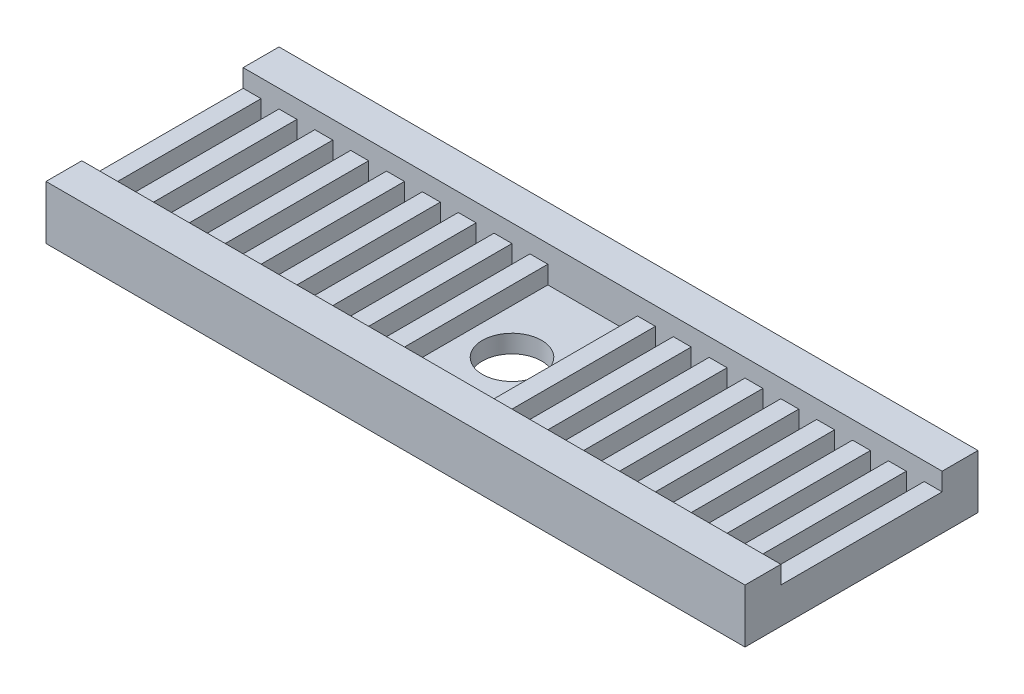
SolidWorks part; units mm, degrees
ref_plane "Front Plane" through (0, 0, 0) normal (0, 0, 1) x (1, 0, 0)
ref_plane "Top Plane" through (0, 0, 0) normal (0, 1, 0) x (1, 0, 0)
ref_plane "Right Plane" through (0, 0, 0) normal (1, 0, 0) x (0, 0, -1)
sketch "Sketch1" plane through (0, 0, 0) normal (0, 1, 0) x (1, 0, 0)
  line L5 (-19.5, -6.5) -> (19.5, -6.5)
  line L6 (-19.5, -6.5) -> (-19.5, 6.5)
  line L15 (-19.5, 6.5) -> (19.5, 6.5)
  line L16 (19.5, -6.5) -> (19.5, 6.5)
  line L17 (-19.5, -6.5) -> (19.5, 6.5) construction
  line L18 (-19.5, 6.5) -> (19.5, -6.5) construction
  point P0 (0, 0)
  dimension "D1" = 13
  dimension "D2" = 39
extrude "Boss-Extrude1" add sketch "Sketch1" along normal blind 3
sketch "Sketch5" plane through (0, 3, 0) normal (0, 1, 0) x (1, 0, 0)
  line L5 (19.5, -6.5) -> (19.5, 6.5) construction
  line L6 (-19.5, -4.5) -> (19.5, -4.5)
  line L8 (-19.5, -4.5) -> (-19.5, 4.5)
  line L9 (-19.5, 4.5) -> (19.5, 4.5)
  line L10 (19.5, -4.5) -> (19.5, 4.5)
  line L11 (-19.5, -4.5) -> (19.5, 4.5) construction
  line L12 (-19.5, 4.5) -> (19.5, -4.5) construction
  point P0 (0, 0)
  dimension "D1" = 9
extrude "Cut-Extrude1" cut sketch "Sketch5" against normal blind 2
sketch "Sketch2" plane through (0, 1, 0) normal (0, 1, 0) x (1, 0, 0)
  line L0 (-19.5, 0) -> (19.5, 0) construction
  line L1 (6.5, -4.5) -> (6.5, 4.5)
  line L2 (6.5, -4.5) -> (5.5, -4.5)
  line L3 (-17.5, -4.5) -> (-17.5, 4.5)
  line L4 (-18.5, -4.5) -> (-19.5, -4.5)
  line L5 (-18.5, -4.5) -> (-18.5, 4.5)
  line L6 (-18.5, 4.5) -> (-19.5, 4.5)
  line L7 (-19.5, -4.5) -> (-19.5, 4.5)
  line L8 (-18.5, -4.5) -> (-19.5, 4.5) construction
  line L9 (-18.5, 4.5) -> (-19.5, -4.5) construction
  line L10 (-17.5, -4.5) -> (-18.5, -4.5)
  line L11 (-18.5, -4.5) -> (-18.5, 4.5)
  line L12 (-17.5, 4.5) -> (-18.5, 4.5)
  line L13 (-16.5, -4.5) -> (-16.5, 4.5)
  line L14 (-16.5, -4.5) -> (-17.5, -4.5)
  line L15 (-17.5, -4.5) -> (-17.5, 4.5)
  line L16 (-16.5, 4.5) -> (-17.5, 4.5)
  line L17 (-15.5, -4.5) -> (-15.5, 4.5)
  line L18 (-15.5, -4.5) -> (-16.5, -4.5)
  line L19 (-16.5, -4.5) -> (-16.5, 4.5)
  line L20 (-15.5, 4.5) -> (-16.5, 4.5)
  line L21 (-14.5, -4.5) -> (-14.5, 4.5)
  line L22 (-14.5, -4.5) -> (-15.5, -4.5)
  line L23 (-15.5, -4.5) -> (-15.5, 4.5)
  line L24 (-14.5, 4.5) -> (-15.5, 4.5)
  line L25 (-13.5, -4.5) -> (-13.5, 4.5)
  line L26 (-13.5, -4.5) -> (-14.5, -4.5)
  line L27 (-14.5, -4.5) -> (-14.5, 4.5)
  line L28 (-13.5, 4.5) -> (-14.5, 4.5)
  line L29 (-12.5, -4.5) -> (-12.5, 4.5)
  line L30 (-12.5, -4.5) -> (-13.5, -4.5)
  line L31 (-13.5, -4.5) -> (-13.5, 4.5)
  line L32 (-12.5, 4.5) -> (-13.5, 4.5)
  line L33 (-11.5, -4.5) -> (-11.5, 4.5)
  line L34 (-11.5, -4.5) -> (-12.5, -4.5)
  line L35 (-12.5, -4.5) -> (-12.5, 4.5)
  line L36 (-11.5, 4.5) -> (-12.5, 4.5)
  line L37 (-10.5, -4.5) -> (-10.5, 4.5)
  line L38 (-10.5, -4.5) -> (-11.5, -4.5)
  line L39 (-11.5, -4.5) -> (-11.5, 4.5)
  line L40 (-10.5, 4.5) -> (-11.5, 4.5)
  line L41 (-9.5, -4.5) -> (-9.5, 4.5)
  line L42 (-9.5, -4.5) -> (-10.5, -4.5)
  line L43 (-10.5, -4.5) -> (-10.5, 4.5)
  line L44 (-9.5, 4.5) -> (-10.5, 4.5)
  line L45 (-8.5, -4.5) -> (-8.5, 4.5)
  line L46 (-8.5, -4.5) -> (-9.5, -4.5)
  line L47 (-9.5, -4.5) -> (-9.5, 4.5)
  line L48 (-8.5, 4.5) -> (-9.5, 4.5)
  line L49 (-7.5, -4.5) -> (-7.5, 4.5)
  line L50 (-7.5, -4.5) -> (-8.5, -4.5)
  line L51 (-8.5, -4.5) -> (-8.5, 4.5)
  line L52 (-7.5, 4.5) -> (-8.5, 4.5)
  line L53 (-6.5, -4.5) -> (-6.5, 4.5)
  line L54 (-6.5, -4.5) -> (-7.5, -4.5)
  line L55 (-7.5, -4.5) -> (-7.5, 4.5)
  line L56 (-6.5, 4.5) -> (-7.5, 4.5)
  line L57 (-5.5, -4.5) -> (-5.5, 4.5)
  line L58 (-5.5, -4.5) -> (-6.5, -4.5)
  line L59 (-6.5, -4.5) -> (-6.5, 4.5)
  line L60 (-5.5, 4.5) -> (-6.5, 4.5)
  line L61 (-4.5, -4.5) -> (-4.5, 4.5)
  line L62 (-4.5, -4.5) -> (-5.5, -4.5)
  line L63 (-5.5, -4.5) -> (-5.5, 4.5)
  line L64 (-4.5, 4.5) -> (-5.5, 4.5)
  line L65 (-3.5, -4.5) -> (-3.5, 4.5)
  line L66 (-3.5, -4.5) -> (-4.5, -4.5)
  line L67 (-4.5, -4.5) -> (-4.5, 4.5)
  line L68 (-3.5, 4.5) -> (-4.5, 4.5)
  line L69 (-2.5, -4.5) -> (-2.5, 4.5)
  line L70 (-2.5, -4.5) -> (-3.5, -4.5)
  line L71 (-3.5, -4.5) -> (-3.5, 4.5)
  line L72 (-2.5, 4.5) -> (-3.5, 4.5)
  line L73 (-1.5, -4.5) -> (-1.5, 4.5)
  line L74 (-1.5, -4.5) -> (-2.5, -4.5)
  line L75 (-2.5, -4.5) -> (-2.5, 4.5)
  line L76 (-1.5, 4.5) -> (-2.5, 4.5)
  line L77 (-0.5, -4.5) -> (-0.5, 4.5)
  line L78 (-0.5, -4.5) -> (-1.5, -4.5)
  line L79 (-1.5, -4.5) -> (-1.5, 4.5)
  line L80 (-0.5, 4.5) -> (-1.5, 4.5)
  line L81 (0.5, -4.5) -> (0.5, 4.5)
  line L82 (0.5, -4.5) -> (-0.5, -4.5)
  line L83 (-0.5, -4.5) -> (-0.5, 4.5)
  line L84 (0.5, 4.5) -> (-0.5, 4.5)
  line L85 (1.5, -4.5) -> (1.5, 4.5)
  line L86 (1.5, -4.5) -> (0.5, -4.5)
  line L87 (0.5, -4.5) -> (0.5, 4.5)
  line L88 (1.5, 4.5) -> (0.5, 4.5)
  line L89 (2.5, -4.5) -> (2.5, 4.5)
  line L90 (2.5, -4.5) -> (1.5, -4.5)
  line L91 (1.5, -4.5) -> (1.5, 4.5)
  line L92 (2.5, 4.5) -> (1.5, 4.5)
  line L93 (3.5, -4.5) -> (3.5, 4.5)
  line L94 (3.5, -4.5) -> (2.5, -4.5)
  line L95 (2.5, -4.5) -> (2.5, 4.5)
  line L96 (3.5, 4.5) -> (2.5, 4.5)
  line L97 (4.5, -4.5) -> (4.5, 4.5)
  line L98 (4.5, -4.5) -> (3.5, -4.5)
  line L99 (3.5, -4.5) -> (3.5, 4.5)
  line L100 (4.5, 4.5) -> (3.5, 4.5)
  line L101 (5.5, -4.5) -> (5.5, 4.5)
  line L102 (5.5, -4.5) -> (4.5, -4.5)
  line L103 (4.5, -4.5) -> (4.5, 4.5)
  line L104 (5.5, 4.5) -> (4.5, 4.5)
  line L105 (5.5, -4.5) -> (5.5, 4.5)
  line L106 (-19.5, 4.5) -> (-19.5, -4.5) construction
  line L107 (6.5, 4.5) -> (5.5, 4.5)
  line L108 (7.5, -4.5) -> (7.5, 4.5)
  line L109 (7.5, -4.5) -> (6.5, -4.5)
  line L110 (6.5, -4.5) -> (6.5, 4.5)
  line L111 (7.5, 4.5) -> (6.5, 4.5)
  line L112 (8.5, -4.5) -> (8.5, 4.5)
  line L113 (8.5, -4.5) -> (7.5, -4.5)
  line L114 (7.5, -4.5) -> (7.5, 4.5)
  line L115 (8.5, 4.5) -> (7.5, 4.5)
  line L116 (9.5, -4.5) -> (9.5, 4.5)
  line L117 (9.5, -4.5) -> (8.5, -4.5)
  line L118 (8.5, -4.5) -> (8.5, 4.5)
  line L119 (9.5, 4.5) -> (8.5, 4.5)
  line L120 (10.5, -4.5) -> (10.5, 4.5)
  line L121 (10.5, -4.5) -> (9.5, -4.5)
  line L122 (9.5, -4.5) -> (9.5, 4.5)
  line L123 (10.5, 4.5) -> (9.5, 4.5)
  line L124 (11.5, -4.5) -> (11.5, 4.5)
  line L125 (11.5, -4.5) -> (10.5, -4.5)
  line L126 (10.5, -4.5) -> (10.5, 4.5)
  line L127 (11.5, 4.5) -> (10.5, 4.5)
  line L128 (12.5, -4.5) -> (12.5, 4.5)
  line L129 (12.5, -4.5) -> (11.5, -4.5)
  line L130 (11.5, -4.5) -> (11.5, 4.5)
  line L131 (12.5, 4.5) -> (11.5, 4.5)
  line L132 (13.5, -4.5) -> (13.5, 4.5)
  line L133 (13.5, -4.5) -> (12.5, -4.5)
  line L134 (12.5, -4.5) -> (12.5, 4.5)
  line L135 (13.5, 4.5) -> (12.5, 4.5)
  line L136 (14.5, -4.5) -> (14.5, 4.5)
  line L137 (14.5, -4.5) -> (13.5, -4.5)
  line L138 (13.5, -4.5) -> (13.5, 4.5)
  line L139 (14.5, 4.5) -> (13.5, 4.5)
  line L140 (15.5, -4.5) -> (15.5, 4.5)
  line L141 (15.5, -4.5) -> (14.5, -4.5)
  line L142 (14.5, -4.5) -> (14.5, 4.5)
  line L143 (15.5, 4.5) -> (14.5, 4.5)
  line L144 (16.5, -4.5) -> (16.5, 4.5)
  line L145 (16.5, -4.5) -> (15.5, -4.5)
  line L146 (15.5, -4.5) -> (15.5, 4.5)
  line L147 (16.5, 4.5) -> (15.5, 4.5)
  line L148 (17.5, -4.5) -> (17.5, 4.5)
  line L149 (17.5, -4.5) -> (16.5, -4.5)
  line L150 (16.5, -4.5) -> (16.5, 4.5)
  line L151 (17.5, 4.5) -> (16.5, 4.5)
  line L152 (18.5, -4.5) -> (18.5, 4.5)
  line L153 (18.5, -4.5) -> (17.5, -4.5)
  line L154 (17.5, -4.5) -> (17.5, 4.5)
  line L155 (18.5, 4.5) -> (17.5, 4.5)
  line L156 (19.5, -4.5) -> (19.5, 4.5)
  line L157 (19.5, -4.5) -> (18.5, -4.5)
  line L158 (18.5, -4.5) -> (18.5, 4.5)
  line L159 (19.5, 4.5) -> (18.5, 4.5)
  line L160 (20.5, -4.5) -> (20.5, 4.5)
  line L161 (20.5, -4.5) -> (19.5, -4.5)
  line L162 (19.5, -4.5) -> (19.5, 4.5)
  line L163 (20.5, 4.5) -> (19.5, 4.5)
  line L164 (19.5, -4.5) -> (19.5, 4.5) construction
  point P2 (-8.5529, 4.5)
  point P3 (-12.5, 0)
  point P4 (-20, 0)
  point P6 (-19, 0)
  point P12 (0, 0)
  point P108 (0, 0)
  point P109 (0, 0)
  point P112 (0, 0)
  point P113 (0, 0)
  point P174 (20, 0)
  dimension "D1" = 1
  dimension "D2" = 9
  dimension "D3" = 40
extrude "Boss-Extrude2" add sketch "Sketch2" along normal blind 1
sketch "Sketch6" plane through (0, 0, 0) normal (0, -1, 0) x (1, 0, 0)
  circle A0 centre (0, 0) radius 1.65
  dimension "D1" = 3.3
extrude "Cut-Extrude2" cut sketch "Sketch6" against normal through all
